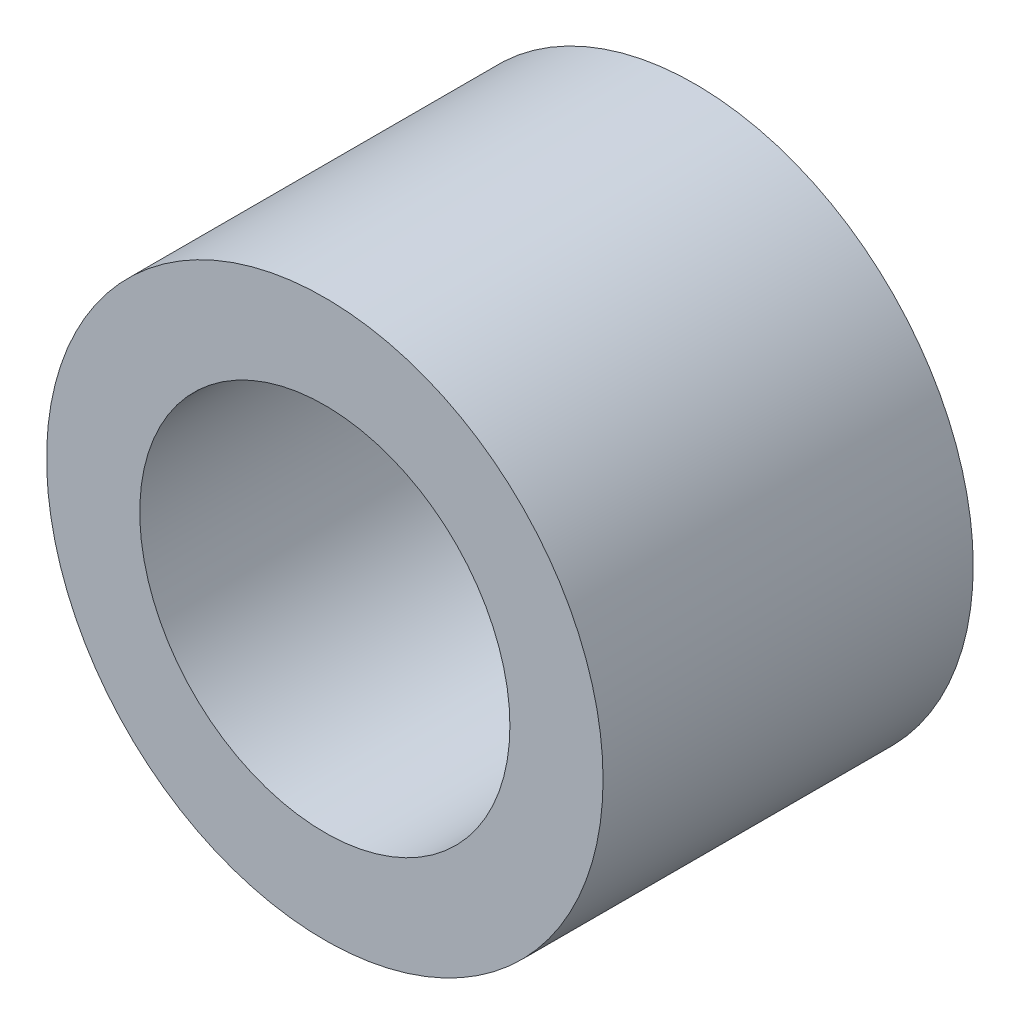
SolidWorks part; units mm, degrees
material "Brass"
ref_plane "Front Plane" through (0, 0, 0) normal (0, 0, 1) x (1, 0, 0)
ref_plane "Top Plane" through (0, 0, 0) normal (0, 1, 0) x (1, 0, 0)
ref_plane "Right Plane" through (0, 0, 0) normal (1, 0, 0) x (0, 0, -1)
sketch "Sketch1" plane through (0, 0, 0) normal (0, 0, 1) x (1, 0, 0)
  circle A0 centre (0, 0) radius 4.51
  circle A1 centre (0, 0) radius 3
  dimension "D1" = 9.02
  dimension "ID" = 6
extrude "Extrude1" add sketch "Sketch1" along normal mid plane 6
sketch "Sketch2" plane through (0, 0, 0) normal (1, 0, 0) x (0, 0, -1)
  line L0 (-3, -3) -> (3, -3) construction
  line L3 (3, 3) -> (-3, 3) construction
  line L5 (-3, -3) -> (3, -3)
  line L6 (3, 3) -> (-3, 3)
sketch "Sketch4" plane through (0, 0, 3) normal (0, 0, 1) x (1, 0, 0)
  line L0 (0, 0) -> (-2.1213, 2.1213)
  line L1 (0, -5.5) -> (0, 5.5) construction
  circle A0 centre (0, 0) radius 3 construction
  dimension "D1" = 45
